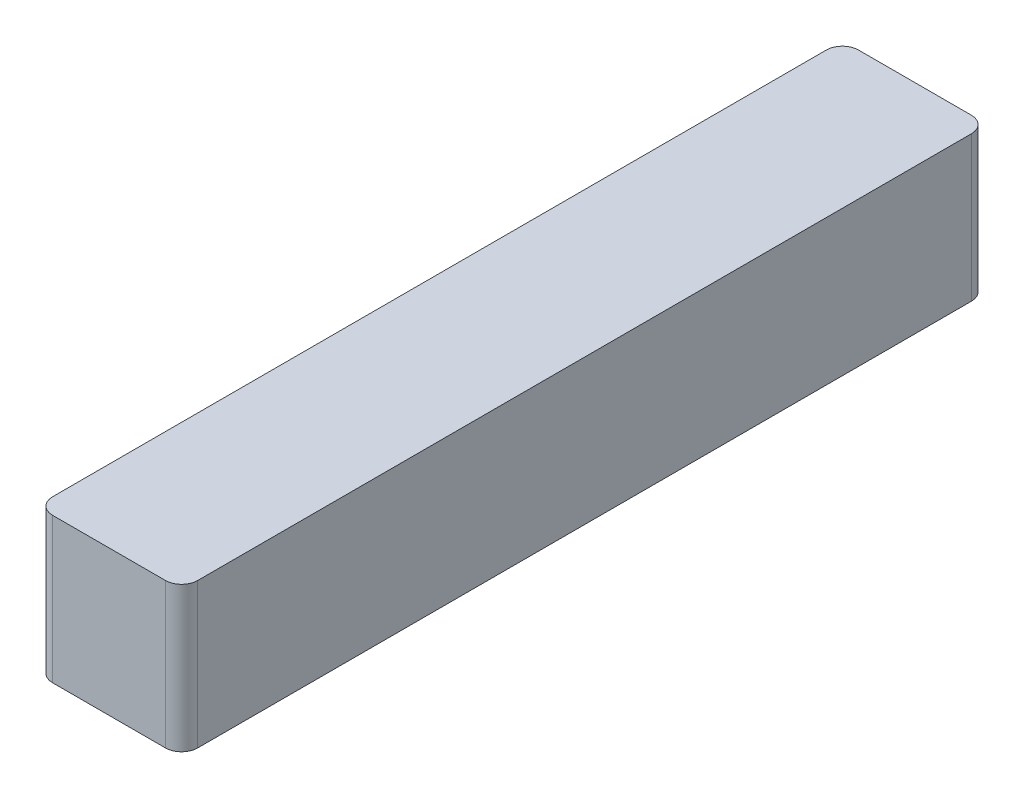
SolidWorks part; units mm, degrees
ref_plane "Front" through (0, 0, 0) normal (0, 0, 1) x (1, 0, 0)
ref_plane "Top" through (0, 0, 0) normal (0, 1, 0) x (1, 0, 0)
ref_plane "Right" through (0, 0, 0) normal (1, 0, 0) x (0, 0, -1)
sketch "Sketch1" plane through (0, 0, 0) normal (0, 0, 1) x (1, 0, 0)
  line L1 (-1.143, 1.143) -> (1.143, 1.143)
  line L2 (-1.143, 1.143) -> (-1.143, -1.143)
  line L3 (-1.143, -1.143) -> (1.143, -1.143)
  line L4 (1.143, 1.143) -> (1.143, -1.143)
  line L5 (-1.143, 1.143) -> (1.143, -1.143) construction
  line L6 (-1.143, -1.143) -> (1.143, 1.143) construction
  point P0 (0, 0)
  dimension "D1" = 2.286
extrude "Boss-Extrude1" add sketch "Sketch1" along normal blind 12.7
fillet "Fillet1" radius 0.254 4 edges at (-1.143, 0, 0) (1.143, 0, 0) (1.143, 0, 12.7) (-1.143, 0, 12.7)
